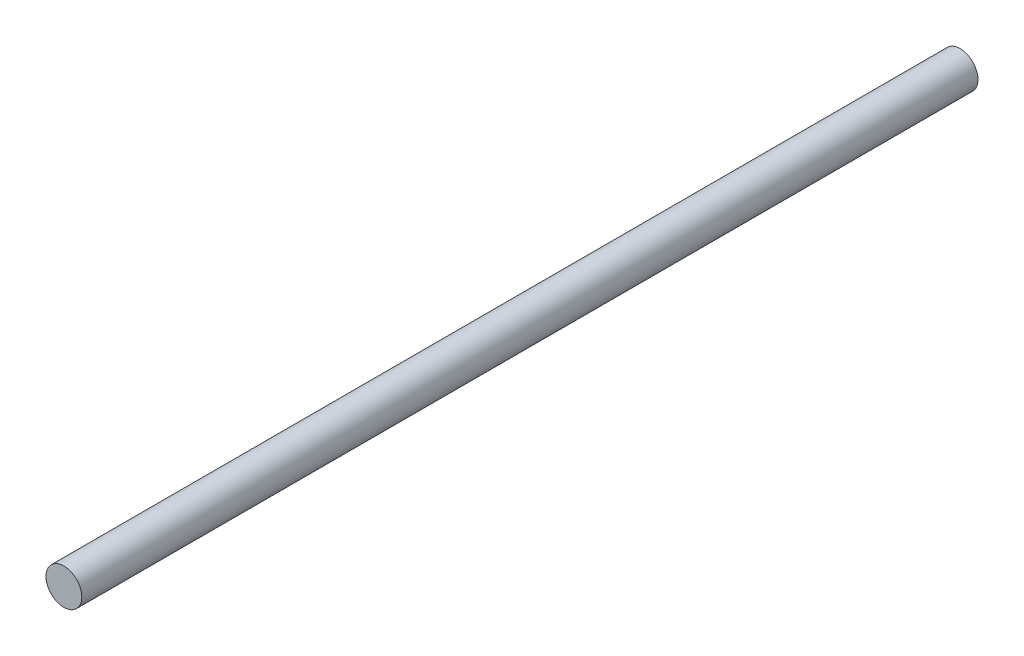
SolidWorks part; units mm, degrees
ref_plane "Ön Düzlem" through (0, 0, 0) normal (0, 0, 1) x (1, 0, 0)
ref_plane "Üst Düzlem" through (0, 0, 0) normal (0, 1, 0) x (1, 0, 0)
ref_plane "Sağ Düzlem" through (0, 0, 0) normal (1, 0, 0) x (0, 0, -1)
sketch "Çizim1" plane through (0, 0, 0) normal (0, 0, 1) x (1, 0, 0)
  circle A0 centre (0, 0) radius 2
  dimension "D1" = 4
extrude "Yükseklik-Ekstrüzyon1" add sketch "Çizim1" along normal blind 100
sketch "Çizim2" plane through (0, 0, 100) normal (0, 0, 1) x (1, 0, 0)
  circle A0 centre (0, 0) radius 2 construction
  point P0 (0, 2)
sketch "Çizim4" plane through (0, 0, 100) normal (0, 0, 1) x (1, 0, 0)
  circle A0 centre (0, 0) radius 4.5
sketch "Çizim5" plane through (0, 0, 0) normal (0, 1, 0) x (1, 0, 0)
  line L0 (-1.5, -100) -> (-2.1, -99.6536)
  line L1 (-2, -100) -> (2, -100) construction
  line L2 (-2.1, -99.6536) -> (-2.1, -100.3464)
  line L3 (-2.1, -100.3464) -> (-1.5, -100)
  line L4 (-2, 0) -> (-2, -100) construction
  dimension "D1" = 0.5
  dimension "D2" = 0.1
  dimension "D3" = 30
  dimension "D4" = 30
